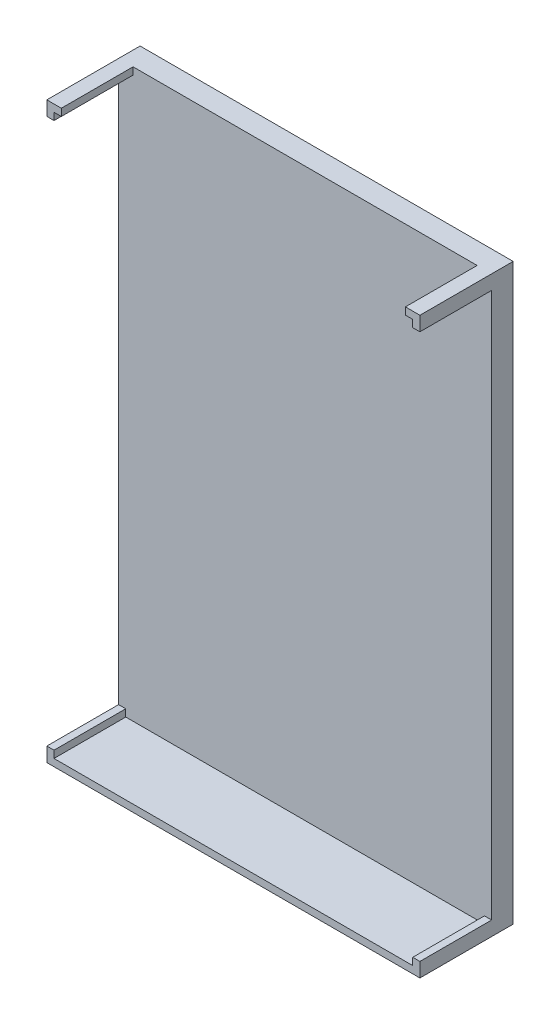
SolidWorks part; units mm, degrees
ref_plane "前视基准面" through (0, 0, 0) normal (0, 0, 1) x (1, 0, 0)
ref_plane "上视基准面" through (0, 0, 0) normal (0, 1, 0) x (1, 0, 0)
ref_plane "右视基准面" through (0, 0, 0) normal (1, 0, 0) x (0, 0, -1)
sketch "草图4" plane through (0, 0, 0) normal (0, 0, 1) x (1, 0, 0)
  line L0 (-26, 38.7965) -> (-25.5906, 38.7965)
  line L1 (26, -40) -> (-26, -40)
  line L2 (26, -40) -> (26, 40)
  line L3 (26, 40) -> (-26, 40)
  line L4 (-26, -40) -> (-26, 40)
  line L5 (26, -40) -> (-26, 40) construction
  line L6 (26, 40) -> (-26, -40) construction
  line L7 (-25.5906, 38.7965) -> (-25.5906, 39.6471)
  line L8 (-25.5906, 39.6471) -> (-24.8761, 39.6471)
  line L9 (-24.8761, 39.6471) -> (-24.8761, 40)
  line L10 (-26, 38.7965) -> (-26, 40)
  line L11 (-26, 40) -> (-24.8761, 40)
  point P0 (0, 0)
  dimension "D1" = 80
  dimension "D2" = 52
extrude "凸台-拉伸3" add sketch "草图4" against normal blind 3 contours L3 L2 L1 L4
sketch "草图6" plane through (0, 0, 0) normal (0, 0, 1) x (1, 0, 0)
  line L0 (-26, 38) -> (-25, 38)
  line L1 (-26, -40) -> (-26, 40) construction
  line L2 (-25, 38) -> (-25, 39)
  line L3 (-25, 39) -> (-23.9789, 39)
  line L4 (-23.9789, 39) -> (-23.9789, 40)
  line L5 (26, 40) -> (-26, 40) construction
  line L6 (-23.9789, 40) -> (-26, 40)
  line L7 (-26, 40) -> (-26, 38)
  line L8 (1.65, 0) -> (-1.65, 0) construction
  line L10 (-26, -38) -> (-25, -38)
  line L11 (-25, -38) -> (-25, -39)
  line L12 (-25, -39) -> (-23.9789, -39)
  line L13 (-23.9789, -39) -> (-23.9789, -40)
  line L14 (-23.9789, -40) -> (-26, -40)
  line L15 (-26, -40) -> (-26, -38)
  line L16 (0, -1.65) -> (0, 1.65) construction
  line L17 (23.9789, -39) -> (23.9789, -40)
  line L18 (23.9789, -40) -> (26, -40)
  line L19 (26, -40) -> (26, -38)
  line L20 (25, -39) -> (23.9789, -39)
  line L21 (25, -38) -> (25, -39)
  line L22 (26, -38) -> (25, -38)
  line L23 (23.9789, 39) -> (23.9789, 40)
  line L24 (23.9789, 40) -> (26, 40)
  line L25 (25, 39) -> (23.9789, 39)
  line L26 (25, 38) -> (25, 39)
  line L27 (26, 38) -> (25, 38)
  line L28 (26, 40) -> (26, 38)
  line M1 (-26, 40) -> (-26, -40)
  line M2 (-26, -40) -> (26, -40)
  line M3 (26, -40) -> (26, 40)
  line M4 (26, 40) -> (-26, 40)
  dimension "D1" = 2
  dimension "D2" = 1
  dimension "D3" = 2.0211
  dimension "D4" = 1
extrude "凸台-拉伸6" add sketch "草图6" along normal blind 10 contours L27 L23 L25 L26 M3 M4 | L13 L12 L11 L10 M1 M2 | L22 L21 L20 L17 M3 M2 | L7 L0 L2 L3 L4 L6
sketch "草图7" plane through (-23.9789, 0, 0) normal (1, 0, 0) x (0, 0, -1)
  line L4 (0, -40) -> (0, -39)
  line L5 (0, -39) -> (-10, -39)
  line L6 (-10, -39) -> (-10, -40)
  line L7 (-10, -40) -> (0, -40)
  line L8 (0, -40) -> (0, -39)
  line L9 (0, -39) -> (-10, -39)
  line L10 (-10, -39) -> (-10, -40)
  line L11 (-10, -40) -> (0, -40)
  dimension "D1" = 0
extrude "凸台-拉伸7" add sketch "草图7" along normal up to next
